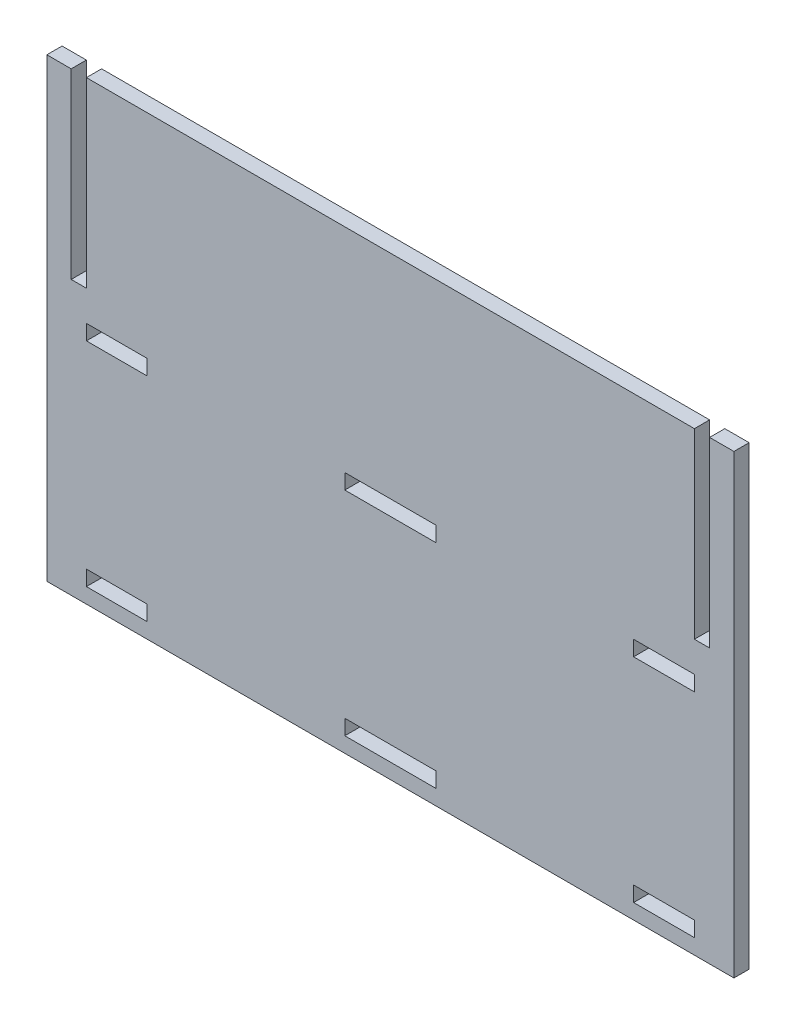
SolidWorks part; units mm, degrees
ref_plane "Plan de face" through (0, 0, 0) normal (0, 0, 1) x (1, 0, 0)
ref_plane "Plan de dessus" through (0, 0, 0) normal (0, 1, 0) x (1, 0, 0)
ref_plane "Plan de droite" through (0, 0, 0) normal (1, 0, 0) x (0, 0, -1)
sketch "Esquisse1" plane through (0, 0, 0) normal (0, 0, 1) x (1, 0, 0)
  line L0 (0, 150) -> (0, 0) construction
  line L1 (80, 10) -> (100, 10)
  line L2 (80, 80) -> (100, 80)
  line L3 (80, 80) -> (80, 75)
  line L4 (80, 75) -> (100, 75)
  line L5 (-100, 150) -> (100, 150)
  line L6 (100, 150) -> (100, 90)
  line L7 (100, 90) -> (105, 90)
  line L8 (105, 90) -> (105, 150)
  line L9 (105, 150) -> (113, 150)
  line L10 (113, 150) -> (113, 0)
  line L11 (113, 0) -> (-113, 0)
  line L12 (100, 80) -> (100, 75)
  line L13 (80, 10) -> (80, 5)
  line L14 (80, 5) -> (100, 5)
  line L15 (100, 10) -> (100, 5)
  line L16 (-15, 5) -> (15, 5)
  line L17 (15, 5) -> (15, 10)
  line L18 (15, 10) -> (0, 10)
  line L19 (-15, 80) -> (0, 80)
  line L20 (0, 80) -> (0, -70) construction
  line L21 (-15, 75) -> (15, 75)
  line L22 (15, 75) -> (15, 80)
  line L23 (15, 80) -> (0, 80)
  line L24 (-15, 75) -> (-15, 80)
  line L25 (113, 80) -> (113, -70) [skipped]
  line L26 (-15, 10) -> (0, 10)
  line L27 (-15, 5) -> (-15, 10)
  line L28 (-100, 10) -> (-100, 5)
  line L29 (-80, 5) -> (-100, 5)
  line L30 (-80, 10) -> (-80, 5)
  line L31 (-100, 80) -> (-100, 75)
  line L32 (-113, 150) -> (-113, 0)
  line L33 (-105, 150) -> (-113, 150)
  line L34 (-105, 90) -> (-105, 150)
  line L35 (-100, 90) -> (-105, 90)
  line L36 (-100, 150) -> (-100, 90)
  line L37 (-80, 75) -> (-100, 75)
  line L38 (-80, 80) -> (-80, 75)
  line L39 (-80, 80) -> (-100, 80)
  line L40 (-80, 10) -> (-100, 10)
  point P33 (0, 75)
  point P36 (0, 5)
  dimension "D2" = 150
  dimension "D3" = 60
  dimension "D4" = 20
  dimension "D5" = 8
  dimension "D6" = 5
  dimension "D7" = 5
  dimension "D8" = 65
  dimension "D9" = 75
  dimension "D10" = 15
  dimension "D11" = 5
  dimension "D12" = 100
  dimension "D13" = 2
extrude "Boss.-Extru.1" add sketch "Esquisse1" along normal blind 5
